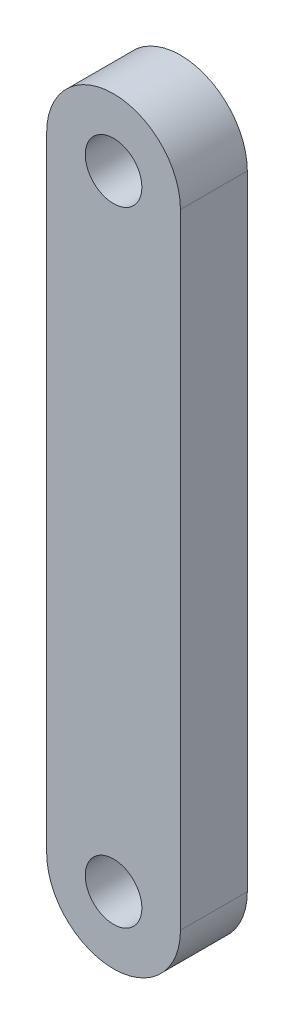
SolidWorks part; units mm, degrees
ref_plane "Front Plane" through (0, 0, 0) normal (0, 0, 1) x (1, 0, 0)
ref_plane "Top Plane" through (0, 0, 0) normal (0, 1, 0) x (1, 0, 0)
ref_plane "Right Plane" through (0, 0, 0) normal (1, 0, 0) x (0, 0, -1)
sketch "Sketch1" plane through (0, 0, 0) normal (0, 0, 1) x (1, 0, 0)
  line L2 (-7.5, 70) -> (-7.5, 0)
  line L4 (7.5, 70) -> (7.5, 0)
  arc A0 (-7.5, 0) -> (7.5, 0) centre (0, 0) ccw
  arc A1 (7.5, 70) -> (-7.5, 70) centre (0, 70) ccw
  circle A2 centre (0, 70) radius 3.175
  circle A3 centre (0, 0) radius 3.175
  dimension "D1" = 7.5
  dimension "D3" = 6.35
  dimension "D2" = 70
extrude "Boss-Extrude1" add sketch "Sketch1" along normal blind 7.5
